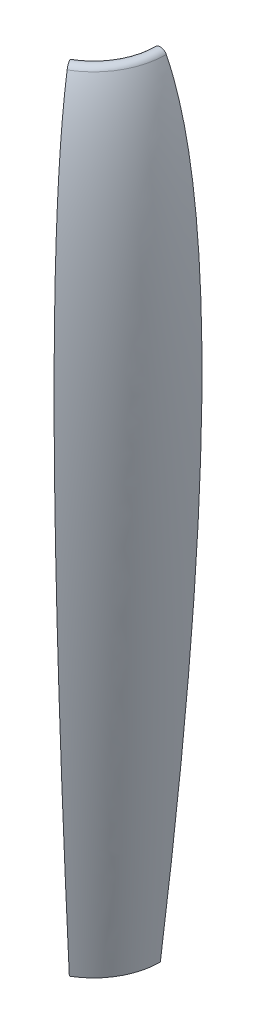
SolidWorks part; units mm, degrees
ref_plane "Front Plane" through (0, 0, 0) normal (0, 0, 1) x (1, 0, 0)
ref_plane "Top Plane" through (0, 0, 0) normal (0, 1, 0) x (1, 0, 0)
ref_plane "Right Plane" through (0, 0, 0) normal (1, 0, 0) x (0, 0, -1)
sketch "Sketch3" plane through (0, 0, 0) normal (0, 0, 1) x (1, 0, 0)
  line L0 (-2.2678, 148.3484) -> (-30.5724, 92.2411) construction
  line L1 (-30.5724, 92.2411) -> (0, -152.4) construction
  line L2 (0, 57.15) -> (0, -6.35) construction
  line L3 (-25.4, 132.1998) -> (-25.4, -65.8414) construction
  line L6 (2.2678, 148.3484) -> (30.5724, 92.2411) construction
  line L7 (30.5724, 92.2411) -> (0, -152.4) construction
  line L8 (3.81, 57.15) -> (3.81, -6.35)
  line L9 (-3.81, 57.15) -> (-3.81, -6.35)
  arc A0 (-2.2678, 148.3484) -> (2.2678, 148.3484) centre (0, 147.2043) cw
  circle A2 centre (0, 82.55) radius 3.175 construction
  circle A3 centre (0, -31.75) radius 3.175 construction
  arc A4 (3.81, 57.15) -> (-3.81, 57.15) centre (0, 57.15) ccw
  arc A5 (-3.81, -6.35) -> (3.81, -6.35) centre (0, -6.35) ccw
  spline S0 degree 2 poles (-2.2678, 148.3484) (-30.5724, 92.2411) (0, -152.4) knots 0 0 0 1 1 1
  spline S1 degree 2 poles (2.2678, 148.3484) (30.5724, 92.2411) (0, -152.4) knots 0 0 0 1 1 1
  point P8 (0, 25.4)
revolve "Main extrude" add sketch "Sketch3" angle 60 about L3
sketch "Sketch4" plane through (-19.05, 0, 10.9985) normal (-0.866, 0, 0.5) x (0.5, 0, 0.866)
  line L0 (16.51, -6.35) -> (16.51, 57.15) construction
  line L1 (16.51, -6.35) -> (16.51, 57.15) construction
  line L4 (12.7, 82.55) -> (12.7, -31.75) construction
  circle A0 centre (12.7, 82.55) radius 3.175
  circle A1 centre (12.7, -31.75) radius 3.175
  point P5 (12.7, 25.4)
  point P7 (16.51, 25.4)
  dimension "D3" = 6.35
  dimension "D1" = 3.81
  dimension "D2" = 114.3
extrude "Spar holes 1" cut sketch "Sketch4" against normal blind 12.7
sketch "Sketch5" plane through (0, 0, 0) normal (0, 0, -1) x (-1, 0, 0)
  line L1 (-3.81, -6.35) -> (-3.81, 57.15) construction
  line L2 (3.81, 57.15) -> (3.81, -6.35) construction
  line L3 (3.81, 57.15) -> (3.81, -6.35) construction
  line L4 (0, 82.55) -> (0, -31.75) construction
  circle A0 centre (0, 82.55) radius 3.175
  circle A1 centre (0, -31.75) radius 3.175
  point P5 (0, 25.4)
  point P11 (3.81, 25.4)
  dimension "D3" = 6.35
  dimension "D1" = 3.81
  dimension "D2" = 114.3
extrude "Spar holes 2" cut sketch "Sketch5" against normal blind 12.7
